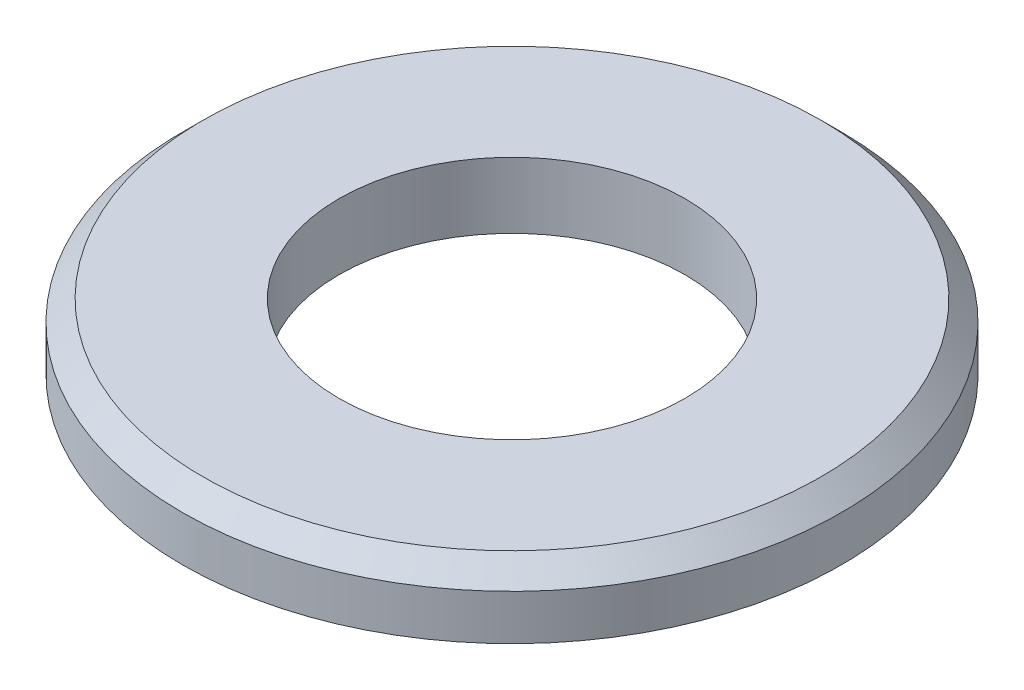
SolidWorks part; units mm, degrees
material "1.0035 (S185)"
ref_plane "Płaszczyzna przednia" through (0, 0, 0) normal (0, 0, 1) x (1, 0, 0)
ref_plane "Płaszczyzna górna" through (0, 0, 0) normal (0, 1, 0) x (1, 0, 0)
ref_plane "Płaszczyzna prawa" through (0, 0, 0) normal (1, 0, 0) x (0, 0, -1)
sketch "Szkic1" plane through (0, 0, 0) normal (0, 0, 1) x (1, 0, 0)
  line L0 (0, 0) -> (0, 4.1503) construction
  line L1 (4.2, 0) -> (8, 0)
  line L2 (4.2, 0) -> (4.2, 1.6)
  line L3 (4.2, 1.6) -> (7.5, 1.6)
  line L4 (8, 0) -> (8, 1.1)
  line L5 (8, 1.1) -> (7.5, 1.6)
  point P1 (8, 1.6)
  dimension "D1" = 8.4
  dimension "D2" = 1.6
  dimension "D3" = 16
  dimension "D4" = 0.5
  dimension "D5" = 45
revolve "Obrót1" add sketch "Szkic1" angle 360 about L0
